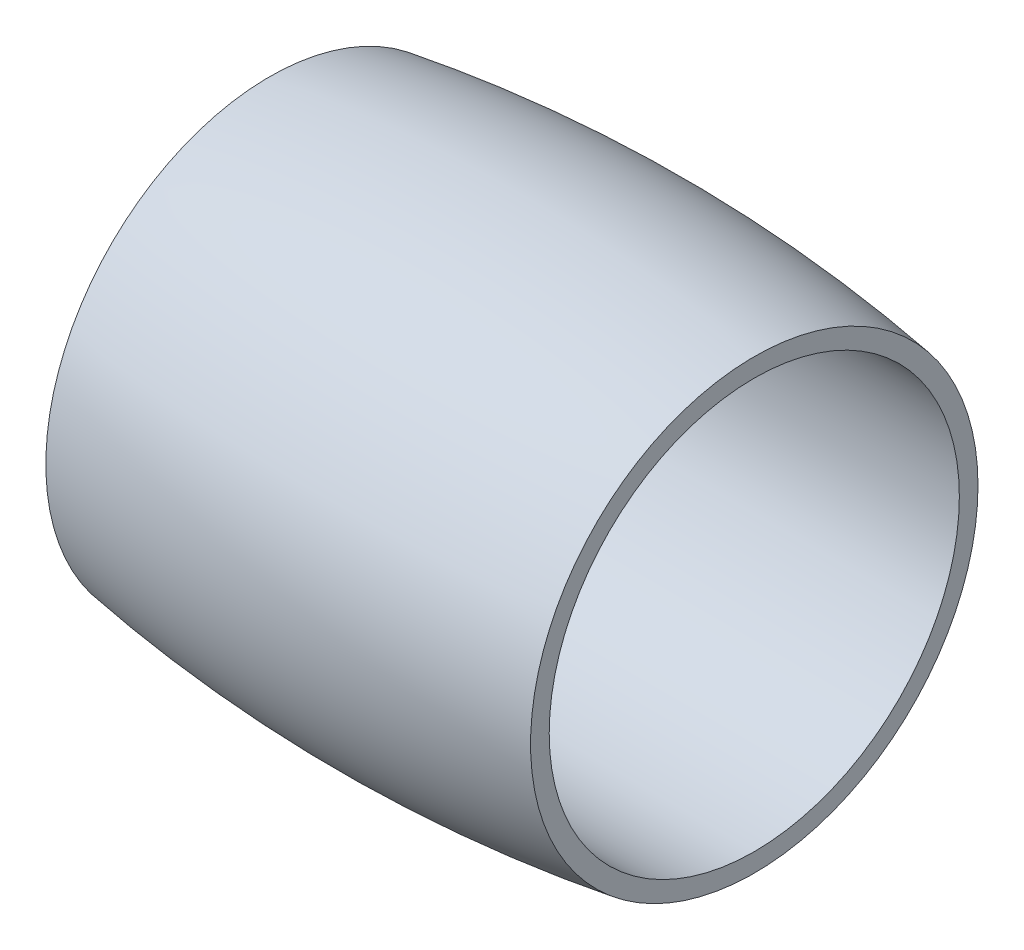
SolidWorks part; units mm, degrees
ref_plane "Ebene vorne" through (0, 0, 0) normal (0, 0, 1) x (1, 0, 0)
ref_plane "Ebene oben" through (0, 0, 0) normal (0, 1, 0) x (1, 0, 0)
ref_plane "Ebene rechts" through (0, 0, 0) normal (1, 0, 0) x (0, 0, -1)
ref_axis "Achse1" through (35.75, 0, 0) along (-1, 0, 0)
sketch "Skizze2" plane through (0, 0, 0) normal (0, 0, 1) x (1, 0, 0)
  line L0 (0, 0) -> (39.5112, 0) construction
  line L1 (-32.5, 27.5) -> (32.5, 27.5)
  line L2 (0, 27.5) -> (0, 0) construction
  line L3 (-32.5, 30) -> (-32.5, 27.5)
  line L4 (32.5, 30) -> (32.5, 27.5)
  line L5 (0, 32.5) -> (0, 27.5) construction
  arc A0 (-32.5, 30) -> (32.5, 30) centre (0, -180) cw
  dimension "Ra" = 65
  dimension "Ri" = 55
  dimension "W" = 65
  dimension "S" = 2.5
revolve "Rotation1" add sketch "Skizze2" angle 360 about axis through (35.75, 0, 0) along (-1, 0, 0)
